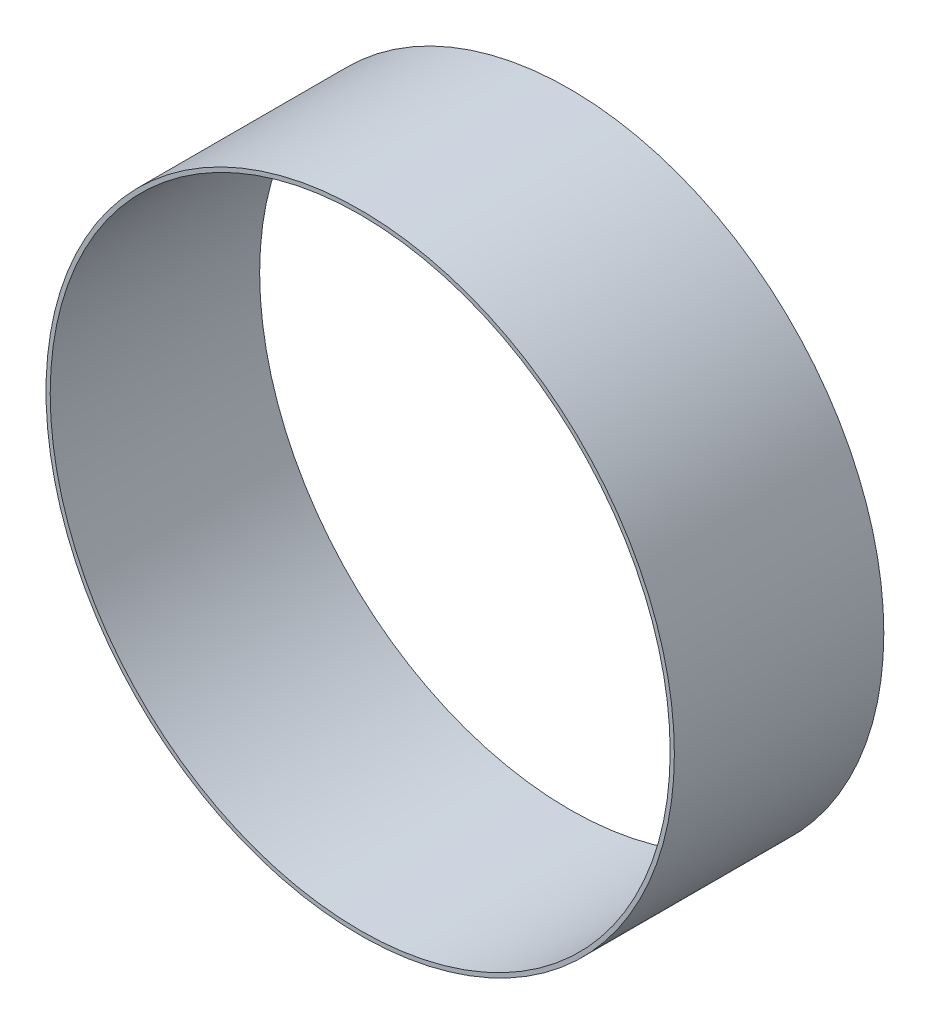
SolidWorks part; units mm, degrees
ref_plane "前视基准面" through (0, 0, 0) normal (0, 0, 1) x (1, 0, 0)
ref_plane "上视基准面" through (0, 0, 0) normal (0, 1, 0) x (1, 0, 0)
ref_plane "右视基准面" through (0, 0, 0) normal (1, 0, 0) x (0, 0, -1)
sketch "草图1" plane through (0, 0, 0) normal (0, 0, 1) x (1, 0, 0)
  circle A0 centre (0, 0) radius 150
  circle A1 centre (0, 0) radius 148
  dimension "D1" = 300
  dimension "D2" = 296
extrude "凸台-拉伸1" add sketch "草图1" along normal blind 100
ref_plane "基准面1" through (0, 0, 0) normal (1, 0, 0) x (0, 0, -1)
ref_plane "基准面2" through (0, 0, 50) normal (0, 0, 1) x (1, 0, 0)
